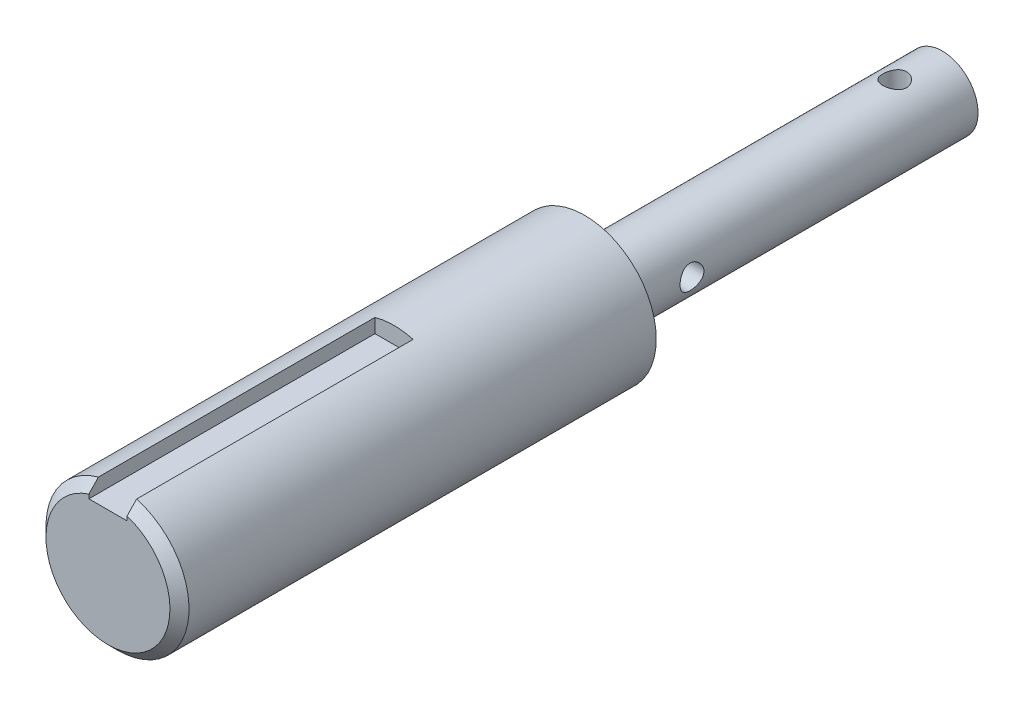
SolidWorks part; units mm, degrees
material "AISI 1020"
ref_plane "Front Plane" through (0, 0, 0) normal (0, 0, 1) x (1, 0, 0)
ref_plane "Top Plane" through (0, 0, 0) normal (0, 1, 0) x (1, 0, 0)
ref_plane "Right Plane" through (0, 0, 0) normal (1, 0, 0) x (0, 0, -1)
sketch "Sketch1" plane through (0, 0, 0) normal (0, 0, 1) x (1, 0, 0)
  circle A0 centre (0, 0) radius 15
  dimension "D1" = 30
extrude "Boss-Extrude1" add sketch "Sketch1" along normal blind 100
sketch "Sketch2" plane through (0, 0, 100) normal (0, 0, 1) x (1, 0, 0)
  line L4 (4, 18.5) -> (-4, 18.5)
  line L5 (4, 18.5) -> (4, 11.5)
  line L6 (4, 11.5) -> (-4, 11.5)
  line L7 (-4, 18.5) -> (-4, 11.5)
  line L8 (4, 18.5) -> (-4, 11.5) construction
  line L9 (4, 11.5) -> (-4, 18.5) construction
  circle A2 centre (0, 0) radius 15 construction
  point P0 (0, 15)
  dimension "D1" = 8
  dimension "D2" = 7
extrude "Cut-Extrude1" cut sketch "Sketch2" against normal blind 60
chamfer "Chamfer1" distance 2 angle 45 1 edges at (0, -15, 100)
scale "Scale1" scale about centroid uniform scaling yes scale factor 2
sketch "Sketch3" plane through (0, 0, -49.4203) normal (0, 0, -1) x (-1, 0, 0)
  circle A0 centre (0, 0) radius 15
  dimension "D1" = 30
extrude "Boss-Extrude2" add sketch "Sketch3" along normal blind 150
sketch "Sketch4" plane through (0, 0, 0) normal (0, 1, 0) x (1, 0, 0)
  line L0 (15, 199.4203) -> (-15, 199.4203) construction
  circle A0 centre (0, 179.4203) radius 5
  dimension "D2" = 10
  dimension "D1" = 20
extrude "Cut-Extrude2" cut sketch "Sketch4" against normal through all both and the other way through all
sketch "Sketch5" plane through (0, 0, 0) normal (1, 0, 0) x (0, 0, -1)
  line L0 (49.4203, -29.699) -> (49.4203, 30.301) construction
  circle A0 centre (79.4203, 0) radius 5
  dimension "D1" = 10
  dimension "D2" = 30
extrude "Cut-Extrude3" cut sketch "Sketch5" against normal through all both and the other way through all
